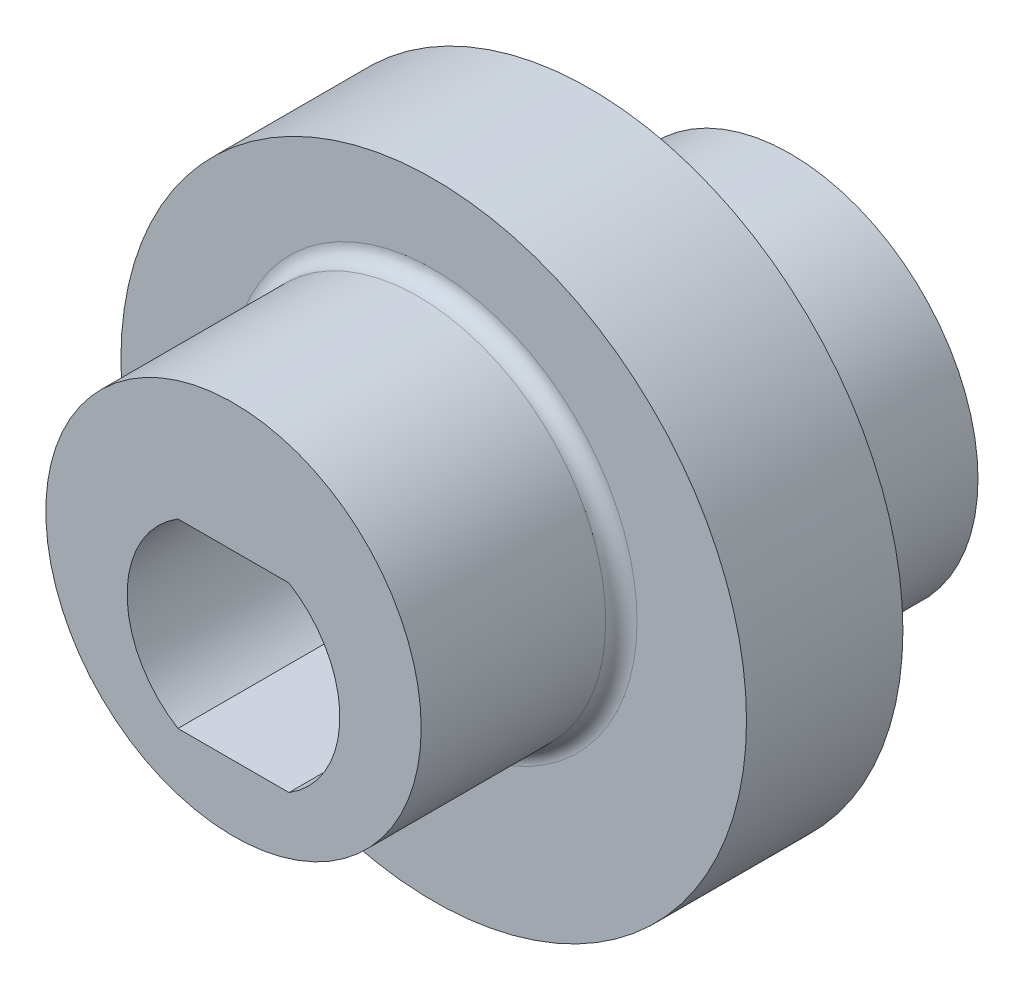
SolidWorks part; units mm, degrees
ref_plane "Front Plane" through (0, 0, 0) normal (0, 0, 1) x (1, 0, 0)
ref_plane "Top Plane" through (0, 0, 0) normal (0, 1, 0) x (1, 0, 0)
ref_plane "Right Plane" through (0, 0, 0) normal (1, 0, 0) x (0, 0, -1)
sketch "Sketch6" plane through (0, 0, 0) normal (0, 0, 1) x (1, 0, 0)
  circle A0 centre (0, 0) radius 10
  dimension "D1" = 20
extrude "Boss-Extrude4" add sketch "Sketch6" along normal mid plane 5
sketch "Sketch7" plane through (0, 0, 2.5) normal (0, 0, 1) x (1, 0, 0)
  circle A0 centre (0, 1) radius 6
  dimension "D1" = 12
  dimension "D2" = 1
extrude "Boss-Extrude5" add sketch "Sketch7" along normal blind 6.4
sketch "Sketch8" plane through (0, 0, -2.5) normal (0, 0, -1) x (-1, 0, 0)
  circle A0 centre (0, -1) radius 6
  dimension "D1" = 12
  dimension "D2" = 1
extrude "Boss-Extrude6" add sketch "Sketch8" along normal blind 6.4
sketch "Sketch11" plane through (0, 0, 2.5) normal (0, 0, 1) x (1, 0, 0)
  line L0 (-1.7748, -2.9) -> (1.7748, -2.9)
  line L1 (-1.6583, -2.5) -> (1.6583, -2.5) construction
  line L2 (-1.6583, -2.5) -> (-1.6583, 2.5) construction
  line L3 (-1.6583, 2.5) -> (1.6583, 2.5) construction
  line L4 (1.6583, -2.5) -> (1.6583, 2.5) construction
  line L5 (-1.6583, -2.5) -> (1.6583, 2.5) construction
  line L6 (-1.6583, 2.5) -> (1.6583, -2.5) construction
  line L7 (-1.7748, 2.9) -> (1.7748, 2.9)
  arc A0 (-1.6583, 2.5) -> (-1.6583, -2.5) centre (0, 0) ccw construction
  arc A1 (1.6583, -2.5) -> (1.6583, 2.5) centre (0, 0) ccw construction
  arc A2 (1.7748, -2.9) -> (1.7748, 2.9) centre (0, 0) ccw
  arc A3 (-1.7748, 2.9) -> (-1.7748, -2.9) centre (0, 0) ccw
  dimension "D1" = 6
  dimension "D2" = 2.5
  dimension "D3" = 0.4
extrude "Cut-Extrude1" cut sketch "Sketch11" against normal through all both and the other way through all
fillet "Fillet1" radius 0.5 2 edges at (6, 1, 2.5) (-6, -1, -2.5)
